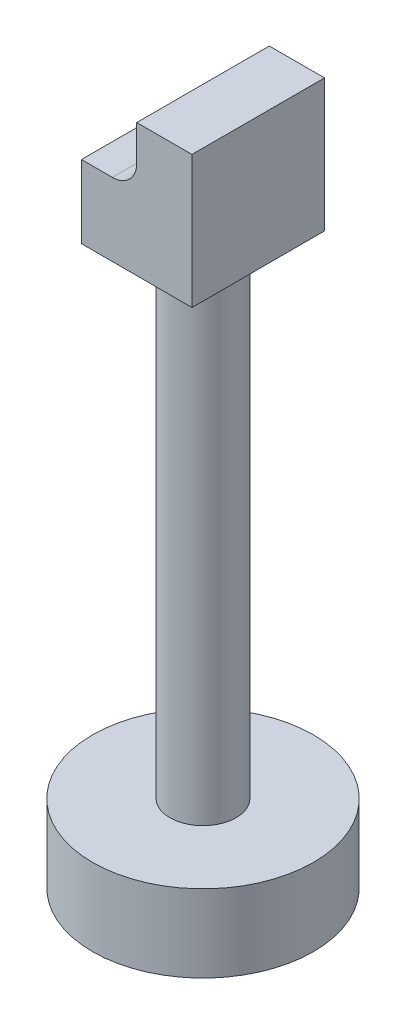
SolidWorks part; units mm, degrees
material "AISI 347 Annealed Stainless Steel (SS)"
ref_plane "Front Plane" through (0, 0, 0) normal (0, 0, 1) x (1, 0, 0)
ref_plane "Top Plane" through (0, 0, 0) normal (0, 1, 0) x (1, 0, 0)
ref_plane "Right Plane" through (0, 0, 0) normal (1, 0, 0) x (0, 0, -1)
sketch "Sketch1" plane through (0, 0, 0) normal (0, 1, 0) x (1, 0, 0)
  circle A0 centre (0, 0) radius 50
  dimension "D1" = 100
extrude "Boss-Extrude1" add sketch "Sketch1" along normal blind 35
sketch "Sketch2" plane through (0, 35, 0) normal (0, 1, 0) x (1, 0, 0)
  circle A0 centre (0, 0) radius 15
extrude "Boss-Extrude2" add sketch "Sketch2" along normal blind 220
sketch "Sketch3" plane through (0, 255, 0) normal (0, 1, 0) x (1, 0, 0)
  line L1 (-25, -30) -> (25, -30)
  line L2 (-25, -30) -> (-25, 30)
  line L3 (-25, 30) -> (25, 30)
  line L4 (25, -30) -> (25, 30)
  line L5 (-25, -30) -> (25, 30) construction
  line L6 (-25, 30) -> (25, -30) construction
  point P0 (0, 0)
  dimension "D1" = 50
  dimension "D2" = 60
extrude "Boss-Extrude3" add sketch "Sketch3" along normal blind 60
sketch "Sketch4" plane through (0, 0, 30) normal (0, 0, 1) x (1, 0, 0)
  line L0 (0, 315) -> (0, 299)
  line L1 (-25, 315) -> (25, 315) construction
  line L2 (-11, 288) -> (-25, 288)
  line L4 (-25, 315) -> (-25, 255) construction
  line L5 (-25, 288) -> (-25, 315)
  line L6 (-25, 315) -> (0, 315)
  arc A0 (-11, 288) -> (0, 299) centre (-11, 299) ccw
  dimension "D1" = 16
extrude "Cut-Extrude1" cut sketch "Sketch4" against normal through all
